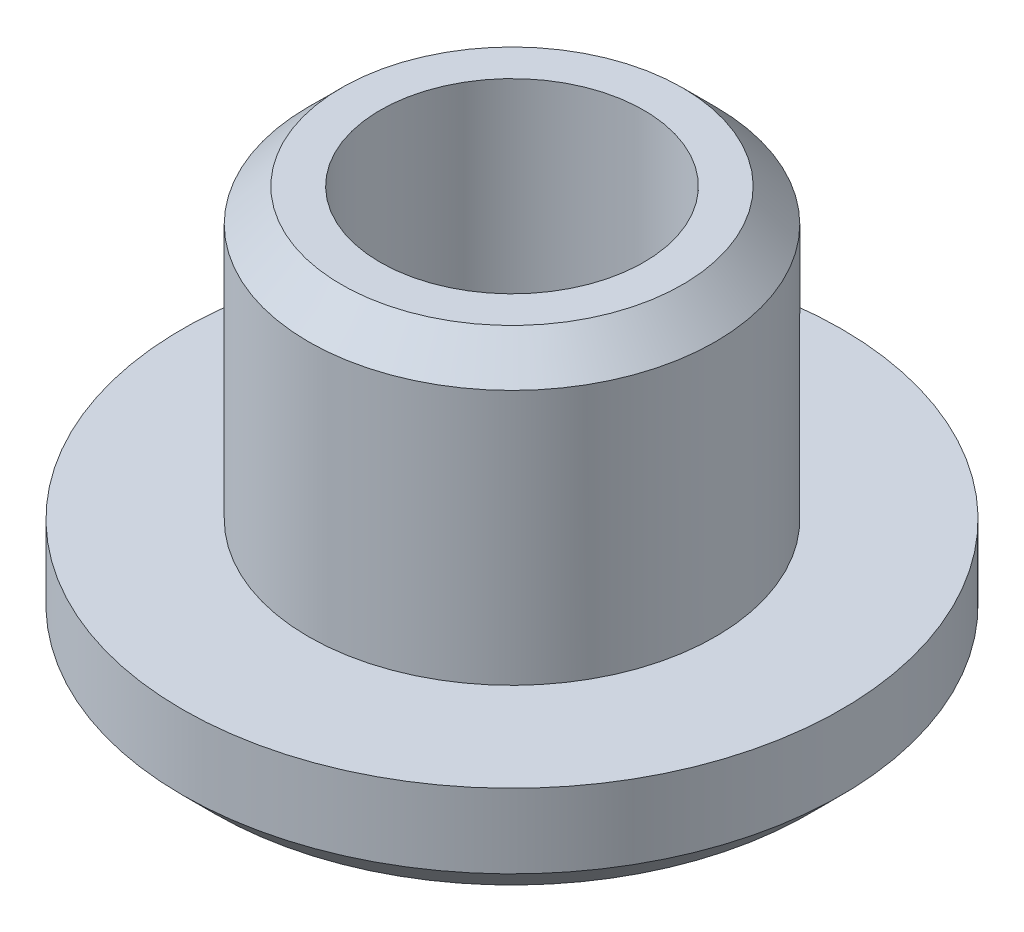
SolidWorks part; units mm, degrees
ref_plane "Plan de face" through (0, 0, 0) normal (0, 0, 1) x (1, 0, 0)
ref_plane "Plan de dessus" through (0, 0, 0) normal (0, 1, 0) x (1, 0, 0)
ref_plane "Plan de droite" through (0, 0, 0) normal (1, 0, 0) x (0, 0, -1)
sketch "Esquisse1" plane through (0, 0, 0) normal (0, 0, 1) x (1, 0, 0)
  line L0 (0, 4.7215) -> (0, -4.6275) construction
  line L1 (1.6, -1.1319) -> (4, -1.1319)
  line L2 (4, -1.1319) -> (4, 0.1681)
  line L3 (4, 0.1681) -> (2.47, 0.1681)
  line L4 (2.47, 0.1681) -> (2.47, 3.6681)
  line L5 (2.47, 3.6681) -> (1.6, 3.6681)
  line L6 (1.6, 3.6681) -> (1.6, -1.1319)
  point P9 (0, 0)
  point P11 (0, 0)
  point P12 (0, 0)
  point P13 (0.2443, -1.1319)
  dimension "D1" = 3.5
  dimension "D2" = 1.3
  dimension "D3" = 1.6
  dimension "D4" = 2.47
  dimension "D5" = 4
revolve "Révolution1" add sketch "Esquisse1" angle 360 about L0
chamfer "Chanfrein1" distance 0.4 angle 45 2 edges at (0, 3.6681, 2.47) (0, -1.1319, 4)
